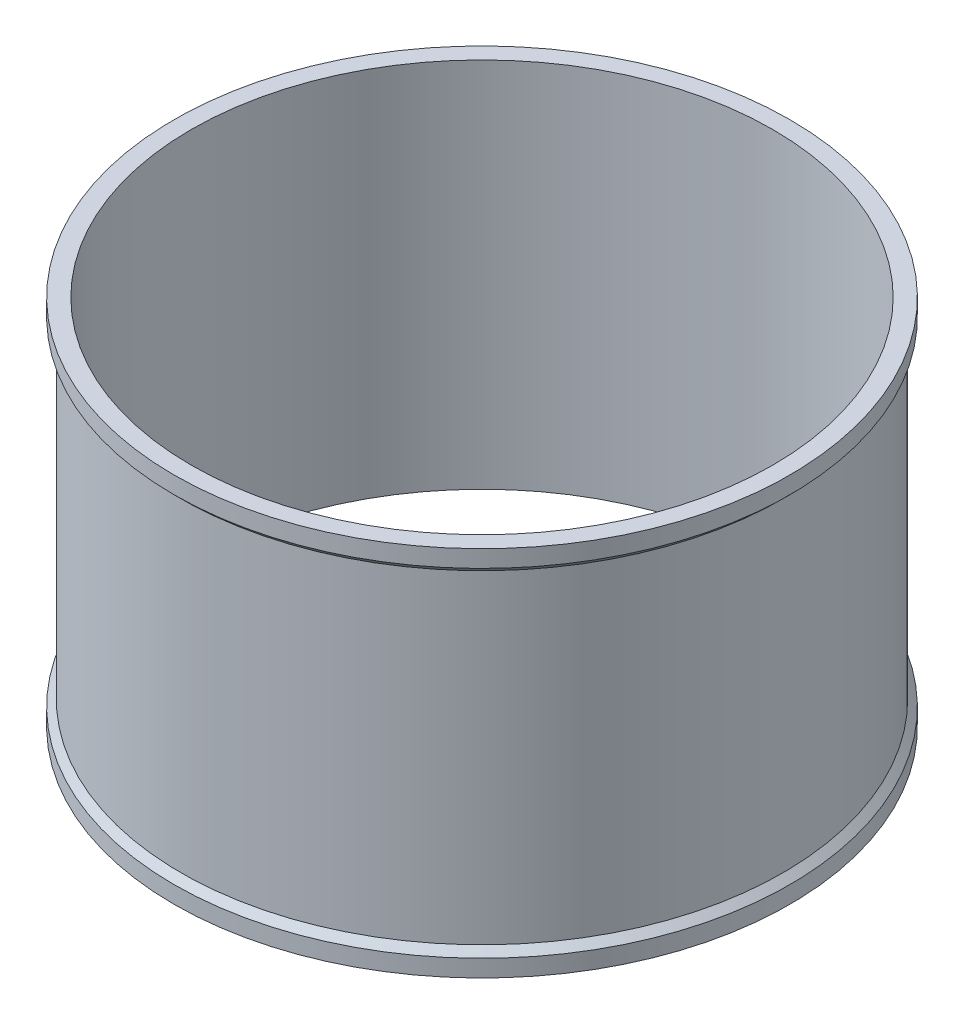
SolidWorks part; units mm, degrees
ref_plane "Front Plane" through (0, 0, 0) normal (0, 0, 1) x (1, 0, 0)
ref_plane "Top Plane" through (0, 0, 0) normal (0, 1, 0) x (1, 0, 0)
ref_plane "Right Plane" through (0, 0, 0) normal (1, 0, 0) x (0, 0, -1)
sketch "Sketch1" plane through (0, 0, 0) normal (0, 0, 1) x (1, 0, 0)
  line L0 (0, 0) -> (85, 0) construction
  line L1 (85, 0) -> (90, 0)
  line L2 (90, 0) -> (90, 5)
  line L4 (88, 7) -> (88, 101.7)
  line L5 (88, 101.7) -> (90, 103.7)
  line L6 (90, 103.7) -> (90, 108.7)
  line L7 (90, 108.7) -> (85, 108.7)
  line L8 (85, 108.7) -> (85, 0)
  line L11 (90, 5) -> (88, 7)
  line L13 (0, 0) -> (0, 108.7) construction
  point P10 (0, 0)
  dimension "D1" = 3
  dimension "D2" = 85
  dimension "D3" = 5
  dimension "D4" = 5
  dimension "D5" = 7
  dimension "D6" = 5
  dimension "D7" = 108.7
  dimension "D8" = 135
revolve "Revolve1" add sketch "Sketch1" angle 360 about L13
